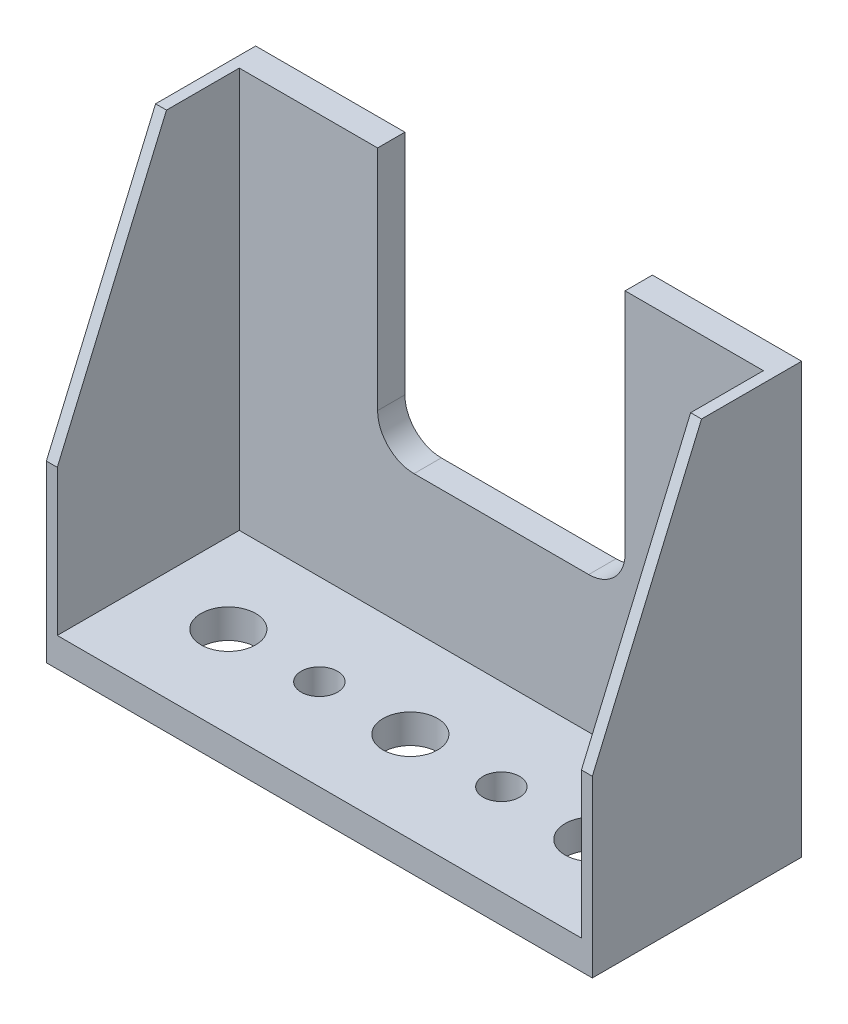
SolidWorks part; units mm, degrees
ref_plane "Front Plane" through (0, 0, 0) normal (0, 0, 1) x (1, 0, 0)
ref_plane "Top Plane" through (0, 0, 0) normal (0, 1, 0) x (1, 0, 0)
ref_plane "Right Plane" through (0, 0, 0) normal (1, 0, 0) x (0, 0, -1)
sketch "Sketch3" plane through (0, 0, 0) normal (0, 0, 1) x (1, 0, 0)
  line L0 (0, -55) -> (0, 55) construction
  line L1 (-15, 11) -> (15, 11)
  line L2 (-15, 11) -> (-15, -11)
  line L3 (-15, -11) -> (15, -11)
  line L4 (15, 11) -> (15, -11)
  line L5 (55, 0) -> (-55, 0) construction
  dimension "D1" = 30
  dimension "D2" = 22
  dimension "D3" = 15
  dimension "D4" = 11
extrude "Boss-Extrude1" add sketch "Sketch3" along normal blind 1.5
sketch "Sketch4" plane through (0, 0, 1.5) normal (0, 0, 1) x (1, 0, 0)
  line L0 (-15, -11) -> (15, -11) construction
  line L1 (-15, 11) -> (-14.4, 11)
  line L2 (-15, 11) -> (-15, -11)
  line L3 (-15, -11) -> (-14.4, -11)
  line L4 (-14.4, 11) -> (-14.4, -11)
  dimension "D1" = 0.6
extrude "Boss-Extrude2" add sketch "Sketch4" along normal blind 10
mirror "Mirror5" about plane through (0, 0, 0) normal (1, 0, 0) of "Boss-Extrude2"
sketch "Sketch5" plane through (-15, 0, 0) normal (-1, 0, 0) x (0, 0, 1)
  line L0 (5.5, 11) -> (11.5, -3)
  line L1 (11.5, 11) -> (0, 11) construction
  line L2 (11.5, 11) -> (11.5, -11) construction
  line L3 (0, -12.1) -> (0, 12.1) construction
  dimension "D1" = 5.5
  dimension "D2" = 8
extrude "Cut-Extrude1" cut sketch "Sketch5" against normal through all and the other way through all
sketch "Sketch6" plane through (0, -11, 0) normal (0, -1, 0) x (1, 0, 0)
  line L0 (12.1, 0) -> (-12.1, 0) construction
  line L1 (-15, 11.5) -> (15, 11.5)
  line L2 (-15, 11.5) -> (-15, 0)
  line L3 (-15, 0) -> (15, 0)
  line L4 (15, 11.5) -> (15, 0)
  line L5 (15, 11.5) -> (15, 0) construction
extrude "Boss-Extrude3" add sketch "Sketch6" along normal blind 1.6
sketch "Sketch7" plane through (0, 0, 1.5) normal (0, 0, 1) x (1, 0, 0)
  line L0 (14.4, 11) -> (-14.4, 11) construction
  line L1 (-6.8, 11) -> (6.8, 11)
  line L2 (-6.8, 11) -> (-6.8, -3.5)
  line L3 (-6.8, -3.5) -> (6.8, -3.5)
  line L4 (6.8, 11) -> (6.8, -3.5)
  line L5 (0, -6.325) -> (0, 6.325) construction
  dimension "D1" = 13.6
  dimension "D2" = 6.8
  dimension "D3" = 14.5
extrude "Cut-Extrude2" cut sketch "Sketch7" against normal blind 1.6
fillet "Fillet1" radius 2 2 edges at (6.8, -3.5, 0.75) (-6.8, -3.5, 0.75)
sketch "Sketch8" plane through (0, -11, 0) normal (0, 1, 0) x (1, 0, 0)
  line L0 (0, -6.325) -> (0, 6.325) construction
  line L1 (-4.8, -1.5) -> (4.8, -1.5) construction
  circle A0 centre (0, -6.5) radius 1.5
  circle A1 centre (-5, -6.5) radius 1
  circle A2 centre (-10, -6.5) radius 1.5
  circle A3 centre (5, -6.5) radius 1
  circle A4 centre (10, -6.5) radius 1.5
  dimension "D1" = 3
  dimension "D2" = 2
  dimension "D3" = 5
  dimension "D4" = 5
  dimension "D5" = 5
  dimension "D6" = 5
  dimension "D7" = 5
extrude "Cut-Extrude3" cut sketch "Sketch8" against normal blind 1.6
